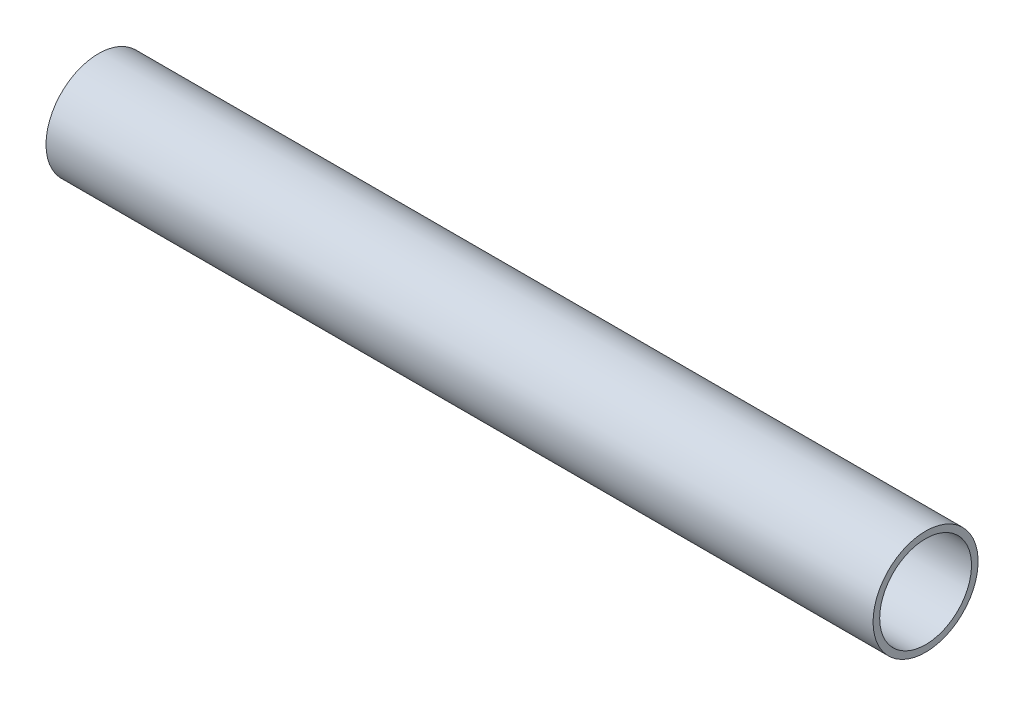
SolidWorks part; units mm, degrees
material "PVC Rígido"
ref_plane "Plano frontal" through (0, 0, 0) normal (0, 0, 1) x (1, 0, 0)
ref_plane "Plano superior" through (0, 0, 0) normal (0, 1, 0) x (1, 0, 0)
ref_plane "Plano direito" through (0, 0, 0) normal (1, 0, 0) x (0, 0, -1)
sketch "Esboço1" plane through (0, 0, 0) normal (0, 0, 1) x (1, 0, 0)
  line L0 (0, 0) -> (0, 38.1) construction
  line L1 (0, 0) -> (600, 0) construction
  line L2 (0, 38.1) -> (600, 38.1)
  line L3 (600, 38.1) -> (600, 33.3)
  line L4 (0, 33.3) -> (0, 38.1)
  line L6 (0, 33.3) -> (600, 33.3)
  dimension "D1" = 76.2
  dimension "D2" = 4.8
  dimension "D5" = 600
revolve "Revolução1" add sketch "Esboço1" angle 360 about L1
